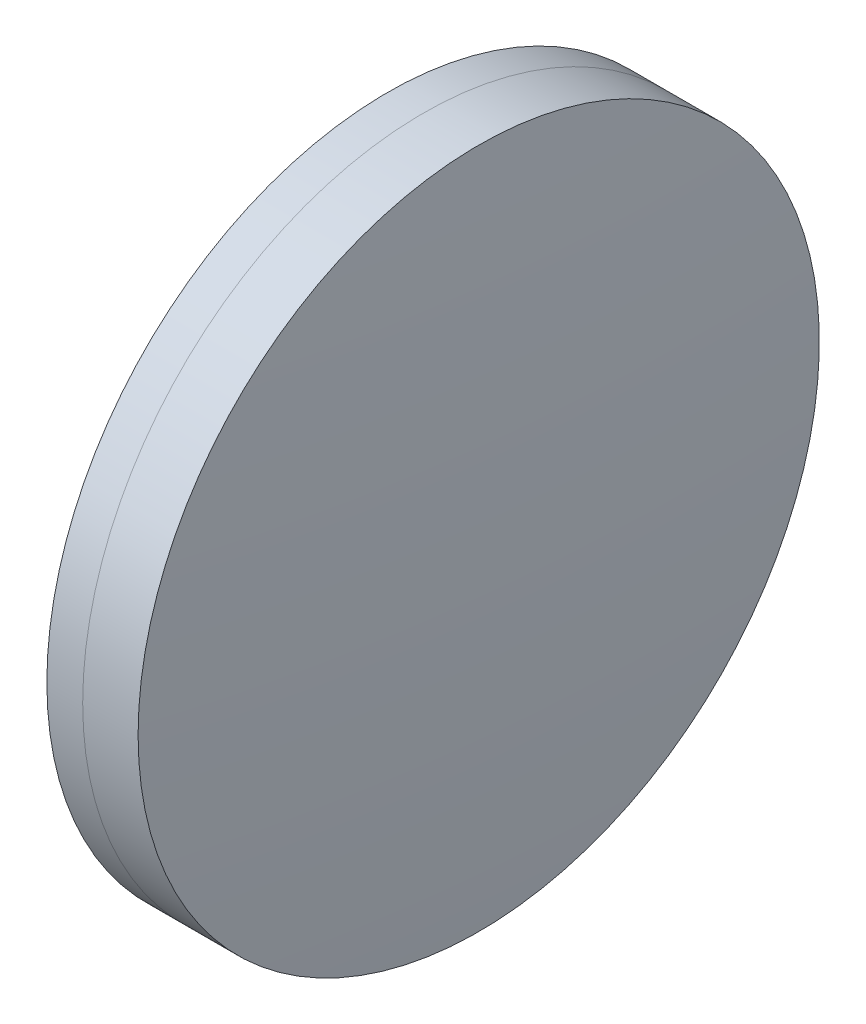
SolidWorks part; units mm, degrees
ref_plane "前视基准面" through (0, 0, 0) normal (0, 0, 1) x (1, 0, 0)
ref_plane "上视基准面" through (0, 0, 0) normal (0, 1, 0) x (1, 0, 0)
ref_plane "右视基准面" through (0, 0, 0) normal (1, 0, 0) x (0, 0, -1)
sketch "草图1" plane through (0, 0, 0) normal (0, 1, 0) x (1, 0, 0)
  line L0 (124.5233, 0) -> (395.1269, 0) construction
  line L1 (244.881, -25) -> (247.5105, -25)
  line L2 (244.881, 25) -> (247.5105, 25)
  arc A0 (247.5105, -25) -> (247.5105, 25) centre (131.8567, 0) ccw
  arc A1 (244.881, 25) -> (244.881, -25) centre (399.4057, 0) ccw
  point P10 (242.8717, 0)
  point P11 (250.1817, 0)
  dimension "D3" = 156.534
  dimension "D4" = 118.325
  dimension "D1" = 25
  dimension "D2" = 25
  dimension "D5" = 7.31
revolve "旋转1" add sketch "草图1" angle 360 about L0
sketch "草图2" plane through (0, 0, 0) normal (0, 1, 0) x (1, 0, 0)
  line L0 (-0.5519, 0) -> (409.4962, 0) construction
  line L2 (247.5105, 25) -> (251.5775, 25)
  line L3 (247.5105, -25) -> (251.5775, -25)
  arc A0 (251.5775, -25) -> (251.5775, 25) centre (-113.8133, 0) ccw
  arc A1 (247.5105, -25) -> (247.5105, 25) centre (131.8567, 0) ccw construction
  arc A2 (247.5105, -25) -> (247.5105, 25) centre (131.8567, 0) ccw
  point P4 (250.1817, 0)
  point P8 (252.4317, 0)
  dimension "D1" = 366.245
  dimension "D2" = 2.25
revolve "旋转3" add sketch "草图2" angle 360 about L0
